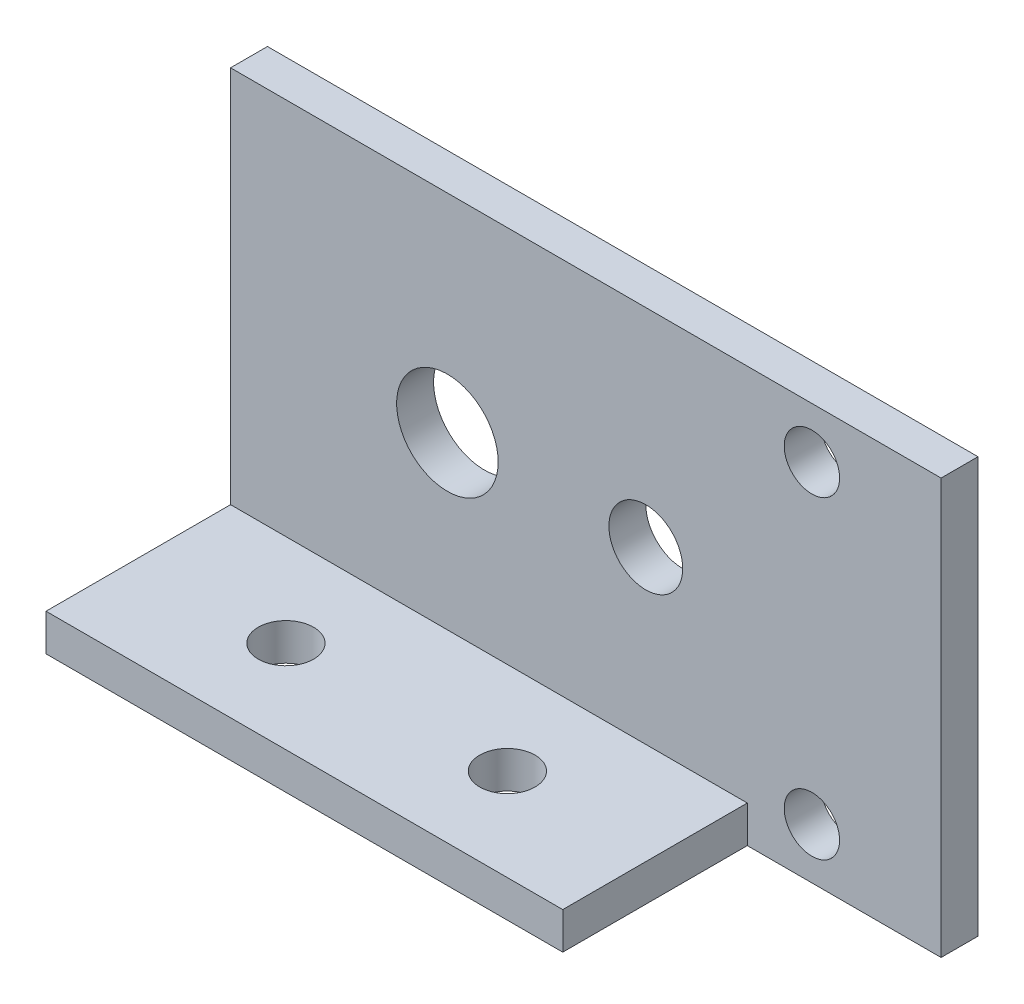
SolidWorks part; units mm, degrees
ref_plane "Спереди" through (0, 0, 0) normal (0, 0, 1) x (1, 0, 0)
ref_plane "Сверху" through (0, 0, 0) normal (0, 1, 0) x (1, 0, 0)
ref_plane "Справа" through (0, 0, 0) normal (1, 0, 0) x (0, 0, -1)
sketch "Sketch1" plane through (0, 0, 0) normal (0, 0, 1) x (1, 0, 0)
  line L2 (-19.25, 11.25) -> (-19.25, -11.25)
  line L3 (-19.25, -11.25) -> (19.25, -11.25)
  line L4 (19.25, 11.25) -> (19.25, -11.25)
  line L5 (-19.25, 11.25) -> (19.25, -11.25) construction
  line L6 (-19.25, -11.25) -> (19.25, 11.25) construction
  line L9 (-19.25, 11.25) -> (19.25, 11.25)
  circle A0 centre (-7.5, 0) radius 2.75
  circle A1 centre (3.25, 0) radius 2
  circle A2 centre (12.25, -8.5) radius 1.5
  circle A3 centre (12.25, 8.5) radius 1.5
  point P0 (0, 0)
  point P14 (0, 0)
  dimension "D7" = 3
  dimension "D11" = 5.5
  dimension "D12" = 4
  dimension "D1" = 38.5
  dimension "D2" = 22.5
  dimension "D3" = 11.75
  dimension "D4" = 10.75
  dimension "D5" = 2.75
  dimension "D6" = 2.75
  dimension "D8" = 7
  dimension "D9" = 7
  dimension "D10" = 11.25
extrude "Boss-Extrude1" add sketch "Sketch1" along normal blind 2
sketch "Sketch2" plane through (-19.25, 0, 0) normal (-1, 0, 0) x (0, 0, 1)
  line L1 (2, -11.25) -> (12, -11.25)
  line L2 (2, -11.25) -> (2, -9.25)
  line L3 (2, -9.25) -> (12, -9.25)
  line L4 (12, -11.25) -> (12, -9.25)
  dimension "D1" = 2
  dimension "D2" = 10
extrude "Boss-Extrude2" add sketch "Sketch2" against normal blind 28
sketch "Sketch3" plane through (19.25, 0, 0) normal (1, 0, 0) x (0, 0, -1)
  line L1 (-2, -11.25) -> (-12, -11.25)
  line L2 (-2, -11.25) -> (-2, -9.25)
  line L3 (-2, -9.25) -> (-12, -9.25)
  line L4 (-12, -11.25) -> (-12, -9.25)
  dimension "D1" = 2
  dimension "D2" = 10
sketch "Sketch4" plane through (0, -9.25, 0) normal (0, 1, 0) x (1, 0, 0)
  line L0 (8.75, -12) -> (-19.25, -12) construction
  line L1 (-19.25, -12) -> (-19.25, -2) construction
  line L2 (8.75, -12) -> (8.75, -2) construction
  circle A0 centre (-11.25, -7) radius 1.5
  circle A1 centre (0.75, -7) radius 1.5
  point P8 (8.75, -7)
  dimension "D1" = 3
  dimension "D2" = 3
  dimension "D3" = 5
  dimension "D4" = 8
  dimension "D5" = 5
  dimension "D6" = 8
extrude "Cut-Extrude1" cut sketch "Sketch4" against normal blind 5
